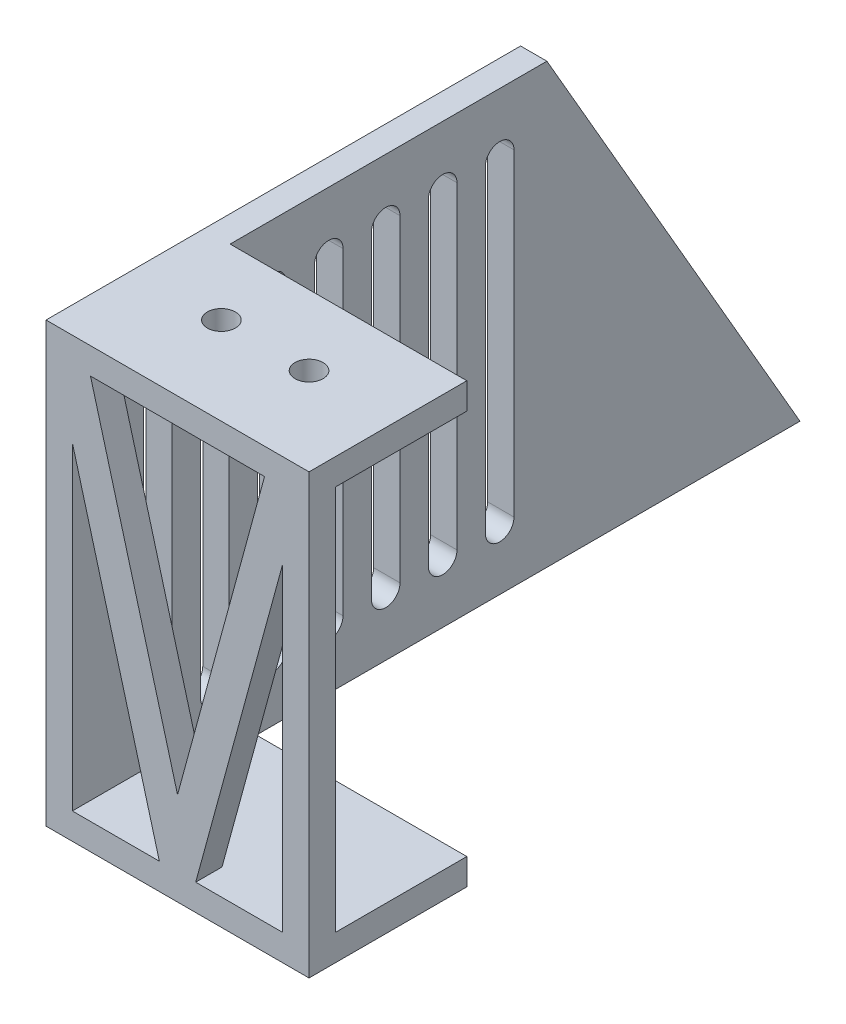
SolidWorks part; units mm, degrees
ref_plane "前视基准面" through (0, 0, 0) normal (0, 0, 1) x (1, 0, 0)
ref_plane "上视基准面" through (0, 0, 0) normal (0, 1, 0) x (1, 0, 0)
ref_plane "右视基准面" through (0, 0, 0) normal (1, 0, 0) x (0, 0, -1)
other "Configuration Table"
sketch "草图1" plane through (0, 0, 0) normal (0, 0, 1) x (1, 0, 0)
  line L0 (-13.5477, 13.2162) -> (-13.5477, -23.1827)
  line L1 (-16.5477, 23.8173) -> (13.4523, 23.8173)
  line L2 (-16.5477, 23.8173) -> (-16.5477, -26.1827)
  line L3 (-16.5477, -26.1827) -> (13.4523, -26.1827)
  line L4 (13.4523, 23.8173) -> (13.4523, -26.1827)
  line L5 (-13.5477, -23.1827) -> (-3.6208, -23.1827)
  line L6 (10.4523, 13.2162) -> (10.4523, -23.1827)
  line L7 (-11.4747, 20.8173) -> (8.3792, 20.8173)
  line L8 (-13.5477, 20.8173) -> (-1.5477, -23.1827) construction
  line L9 (-1.5477, -23.1827) -> (10.4523, 20.8173) construction
  line L10 (-13.5477, 13.2162) -> (-3.6208, -23.1827)
  line L12 (-11.4747, 20.8173) -> (-1.5477, -15.5815)
  line L13 (-1.5477, -15.5815) -> (8.3792, 20.8173)
  line L14 (-15.4773, 20.2911) -> (-1.5477, -30.7838) construction
  line L15 (-13.5477, 20.8173) -> (10.4523, 20.8173) construction
  line L16 (-13.5477, 20.8173) -> (-13.5477, -23.1827) construction
  line L17 (-11.6182, 21.3436) -> (-1.5477, -15.5815) construction
  line L18 (-1.5477, -15.5815) -> (8.5227, 21.3436) construction
  line L19 (10.4523, 20.8173) -> (10.4523, -23.1827) construction
  line L20 (-1.5477, -30.7838) -> (12.3818, 20.2911) construction
  line L22 (0.5253, -23.1827) -> (10.4523, 13.2162)
  line L23 (0.5253, -23.1827) -> (10.4523, -23.1827)
  line L24 (-13.5477, -23.1827) -> (10.4523, -23.1827) construction
  dimension "D1" = 30
  dimension "D2" = 50
  dimension "D4" = 2
  dimension "D3" = 3
  dimension "D5" = 2
extrude "凸台-拉伸1" add sketch "草图1" along normal blind 3
sketch "草图2" plane through (-16.5477, 0, 0) normal (-1, 0, 0) x (0, 0, 1)
  line L0 (3, 23.8173) -> (0, 23.8173) construction
  line L1 (0, -26.1827) -> (-80, -26.1827)
  line L3 (0, 23.8173) -> (-51.1325, 23.8173)
  line L9 (0, -26.1827) -> (0, 23.8173)
  line L10 (0, 23.8173) -> (0, -26.1827) construction
  line L11 (3, -26.1827) -> (0, -26.1827) construction
  line L12 (-80, -26.1827) -> (-51.1325, 23.8173)
  line L17 (-3, -23.1827) -> (-74.8038, -23.1827)
  line L18 (-74.8038, -23.1827) -> (-49.4004, 20.8173)
  line L19 (-3, 20.8173) -> (-49.4004, 20.8173)
  line L20 (-3, -23.1827) -> (-3, 20.8173)
  line L21 (-3, -1.1827) -> (-62.1021, -1.1827) construction
  line L22 (-45.7465, 16.9352) -> (-45.7465, -19.3371) construction
  line L23 (-44.1147, 16.9352) -> (-44.1147, -19.3371)
  line L24 (-47.3782, 16.9352) -> (-47.3782, -19.3371)
  line L25 (-40.8782, 16.9352) -> (-40.8782, -19.3371)
  line L26 (-37.6147, 16.9352) -> (-37.6147, -19.3371)
  line L27 (-39.2465, 16.9352) -> (-39.2465, -19.3371) construction
  line L28 (-34.3782, 16.9352) -> (-34.3782, -19.3371)
  line L29 (-31.1147, 16.9352) -> (-31.1147, -19.3371)
  line L30 (-32.7465, 16.9352) -> (-32.7465, -19.3371) construction
  line L31 (-27.8782, 16.9352) -> (-27.8782, -19.3371)
  line L32 (-24.6147, 16.9352) -> (-24.6147, -19.3371)
  line L33 (-26.2465, 16.9352) -> (-26.2465, -19.3371) construction
  line L34 (-21.3782, 16.9352) -> (-21.3782, -19.3371)
  line L35 (-18.1147, 16.9352) -> (-18.1147, -19.3371)
  line L36 (-19.7465, 16.9352) -> (-19.7465, -19.3371) construction
  line L37 (-14.8782, 16.9352) -> (-14.8782, -19.3371)
  line L38 (-11.6147, 16.9352) -> (-11.6147, -19.3371)
  line L39 (-13.2465, 16.9352) -> (-13.2465, -19.3371) construction
  line L40 (-8.3782, 16.9352) -> (-8.3782, -19.3371)
  line L41 (-5.1147, 16.9352) -> (-5.1147, -19.3371)
  line L42 (-6.7465, 16.9352) -> (-6.7465, -19.3371) construction
  arc A1 (-44.1147, 16.9352) -> (-47.3782, 16.9352) centre (-45.7465, 16.9352) ccw
  arc A2 (-47.3782, -19.3371) -> (-44.1147, -19.3371) centre (-45.7465, -19.3371) ccw
  arc A3 (-37.6147, 16.9352) -> (-40.8782, 16.9352) centre (-39.2465, 16.9352) ccw
  arc A4 (-40.8782, -19.3371) -> (-37.6147, -19.3371) centre (-39.2465, -19.3371) ccw
  arc A5 (-31.1147, 16.9352) -> (-34.3782, 16.9352) centre (-32.7465, 16.9352) ccw
  arc A6 (-34.3782, -19.3371) -> (-31.1147, -19.3371) centre (-32.7465, -19.3371) ccw
  arc A7 (-24.6147, 16.9352) -> (-27.8782, 16.9352) centre (-26.2465, 16.9352) ccw
  arc A8 (-27.8782, -19.3371) -> (-24.6147, -19.3371) centre (-26.2465, -19.3371) ccw
  arc A9 (-18.1147, 16.9352) -> (-21.3782, 16.9352) centre (-19.7465, 16.9352) ccw
  arc A10 (-21.3782, -19.3371) -> (-18.1147, -19.3371) centre (-19.7465, -19.3371) ccw
  arc A11 (-11.6147, 16.9352) -> (-14.8782, 16.9352) centre (-13.2465, 16.9352) ccw
  arc A12 (-14.8782, -19.3371) -> (-11.6147, -19.3371) centre (-13.2465, -19.3371) ccw
  arc A13 (-5.1147, 16.9352) -> (-8.3782, 16.9352) centre (-6.7465, 16.9352) ccw
  arc A14 (-8.3782, -19.3371) -> (-5.1147, -19.3371) centre (-6.7465, -19.3371) ccw
  point P18 (-45.7465, -1.2009)
  point P23 (-45.7465, -19.3371)
  point P27 (-39.2465, -1.2009)
  point P34 (-32.7465, -1.2009)
  point P41 (-26.2465, -1.2009)
  point P48 (-19.7465, -1.2009)
  point P55 (-13.2465, -1.2009)
  point P62 (-6.7465, -1.2009)
  line M9 (0, 23.8173) -> (0, -26.1827)
  dimension "D4" = 7
  dimension "D1" = 80
  dimension "D2" = 60
  dimension "D3" = 3
extrude "凸台-拉伸3" add sketch "草图2" against normal blind 3 contours L12 L1 L3 L20 L17 L18 L19 M9 | L17 L20 L19 L18 A14 L40 A13 L41 A12 L37 A11 L38 A10 L34 A9 L35 A8 L31 A7 L32 A6 L28 A5 L29 A4 L25 A3 L26 A2 L24 A1 L23
sketch "草图3" plane through (0, 23.8173, 0) normal (0, 1, 0) x (1, 0, 0)
  line L0 (13.4523, 0) -> (-13.5477, 0) construction
  line L1 (-13.5477, 15) -> (13.4523, 15)
  line L2 (-13.5477, 15) -> (-13.5477, 0)
  line L3 (-13.5477, 0) -> (13.4523, 0)
  line L4 (13.4523, 15) -> (13.4523, 0)
  line L5 (-13.5477, 0) -> (-13.5477, 51.1325) construction
  line L6 (13.4523, -3) -> (13.4523, 0) construction
  line L7 (-6.5477, 7) -> (3.4523, 7) construction
  line L8 (-16.5477, -3) -> (-16.5477, 51.1325) construction
  line L10 (13.4523, -3) -> (-16.5477, -3) construction
  circle A0 centre (-6.5477, 7) radius 1.6
  circle A1 centre (3.4523, 7) radius 1.6
  dimension "D2" = 10
  dimension "D5" = 3.2
  dimension "D1" = 15
  dimension "D3" = 10
  dimension "D4" = 10
extrude "凸台-拉伸4" add sketch "草图3" along normal blind 3 from surface at -50 starting at face at (-5.5477, -26.1827, -25.6667)
sketch "草图5" plane through (0, 23.8173, 0) normal (0, 1, 0) x (1, 0, 0)
  line L1 (-13.5477, 15) -> (13.4523, 15)
  line L2 (-13.5477, 15) -> (-13.5477, 0)
  line L3 (-13.5477, 0) -> (13.4523, 0)
  line L4 (13.4523, 15) -> (13.4523, 0)
  circle A0 centre (-6.5477, 7) radius 1.6
  circle A1 centre (3.4523, 7) radius 1.6
  circle A2 centre (-6.5477, 7) radius 1.6 construction
extrude "凸台-拉伸5" add sketch "草图5" against normal blind 3
